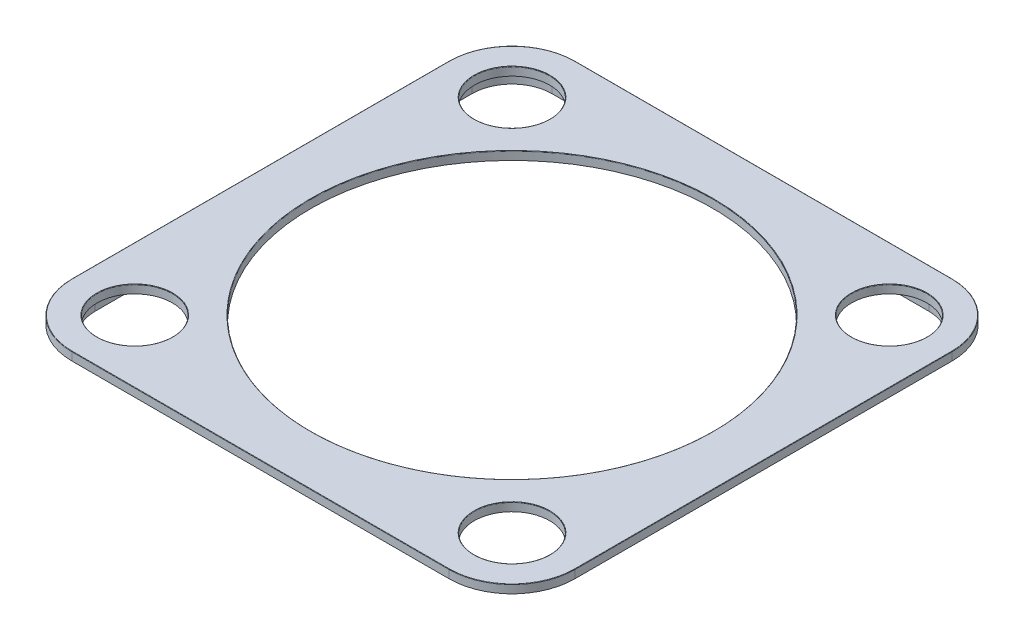
SolidWorks part; units mm, degrees
ref_plane "Front Plane" through (0, 0, 0) normal (0, 0, 1) x (1, 0, 0)
ref_plane "Top Plane" through (0, 0, 0) normal (0, 1, 0) x (1, 0, 0)
ref_plane "Right Plane" through (0, 0, 0) normal (1, 0, 0) x (0, 0, -1)
sketch "Sketch1" plane through (0, 0, 0) normal (0, 1, 0) x (1, 0, 0)
  line L1 (-450, -600) -> (450, -600)
  line L2 (-600, -450) -> (-600, 450)
  line L3 (-450, 600) -> (450, 600)
  line L4 (600, -450) -> (600, 450)
  line L5 (-600, -600) -> (600, 600) construction
  line L6 (-600, 600) -> (600, -600) construction
  arc A0 (450, 600) -> (600, 450) centre (450, 450) cw
  arc A1 (600, -450) -> (450, -600) centre (450, -450) cw
  arc A2 (-450, -600) -> (-600, -450) centre (-450, -450) cw
  arc A3 (-600, 450) -> (-450, 600) centre (-450, 450) cw
  point P0 (0, 0)
  dimension "D3" = 150
  dimension "D1" = 1200
  dimension "D2" = 1200
extrude "Boss-Extrude1" add sketch "Sketch1" along normal blind 20
sketch "Sketch2" plane through (0, 0, 0) normal (0, -1, 0) x (1, 0, 0)
  line L8 (560, -450) -> (560, 450)
  line L9 (450, 560) -> (-450, 560)
  line L10 (-560, 450) -> (-560, -450)
  line L11 (-450, -560) -> (450, -560)
  line L12 (560, -450) -> (560, 450)
  line L13 (450, 560) -> (-450, 560)
  line L14 (-560, 450) -> (-560, -450)
  line L15 (-450, -560) -> (450, -560)
  line L16 (545, -450) -> (545, 450)
  line L17 (450, 545) -> (-450, 545)
  line L18 (-545, 450) -> (-545, -450)
  line L19 (-450, -545) -> (450, -545)
  line L20 (545, -450) -> (545, 450)
  line L21 (450, 545) -> (-450, 545)
  line L22 (-545, 450) -> (-545, -450)
  line L23 (-450, -545) -> (450, -545)
  arc A8 (450, -560) -> (560, -450) centre (450, -450) ccw
  arc A9 (560, 450) -> (450, 560) centre (450, 450) ccw
  arc A10 (-450, 560) -> (-560, 450) centre (-450, 450) ccw
  arc A11 (-560, -450) -> (-450, -560) centre (-450, -450) ccw
  arc A12 (450, -560) -> (560, -450) centre (450, -450) ccw
  arc A13 (560, 450) -> (450, 560) centre (450, 450) ccw
  arc A14 (-450, 560) -> (-560, 450) centre (-450, 450) ccw
  arc A15 (-560, -450) -> (-450, -560) centre (-450, -450) ccw
  arc A16 (450, -545) -> (545, -450) centre (450, -450) ccw
  arc A17 (545, 450) -> (450, 545) centre (450, 450) ccw
  arc A18 (-450, 545) -> (-545, 450) centre (-450, 450) ccw
  arc A19 (-545, -450) -> (-450, -545) centre (-450, -450) ccw
  arc A20 (450, -545) -> (545, -450) centre (450, -450) ccw
  arc A21 (545, 450) -> (450, 545) centre (450, 450) ccw
  arc A22 (-450, 545) -> (-545, 450) centre (-450, 450) ccw
  arc A23 (-545, -450) -> (-450, -545) centre (-450, -450) ccw
  dimension "D1" = 40
  dimension "D2" = 55
sketch "Sketch3" plane through (0, 20, 0) normal (0, 1, 0) x (1, 0, 0)
  circle A0 centre (-450, 450) radius 90
  circle A1 centre (450, 450) radius 90
  circle A2 centre (-450, -450) radius 90
  circle A3 centre (450, -450) radius 90
  dimension "D1" = 180
  dimension "D2" = 180
  dimension "D3" = 180
  dimension "D4" = 180
extrude "Cut-Extrude1" cut sketch "Sketch3" against normal through all
sketch "Sketch4" plane through (0, 20, 0) normal (0, 1, 0) x (1, 0, 0)
  circle A0 centre (0, 0) radius 480
  dimension "D1" = 960
extrude "Cut-Extrude2" cut sketch "Sketch4" against normal through all
extrude "Boss-Extrude2" add sketch "Sketch2" along normal blind 20
fillet "Fillet1" radius 1 8 edges at (-556.066, 20, -556.066) (0, 20, -600) (556.066, 20, -556.066) (600, 20, 0) (556.066, 20, 556.066) (0, 20, 600) (-556.066, 20, 556.066) (-600, 20, 0)
fillet "Fillet2" radius 1 1 edges at (0, 20, 480)
fillet "Fillet3" radius 1 4 edges at (450, 20, -360) (-450, 20, -360) (-450, 20, 540) (450, 20, 540)
